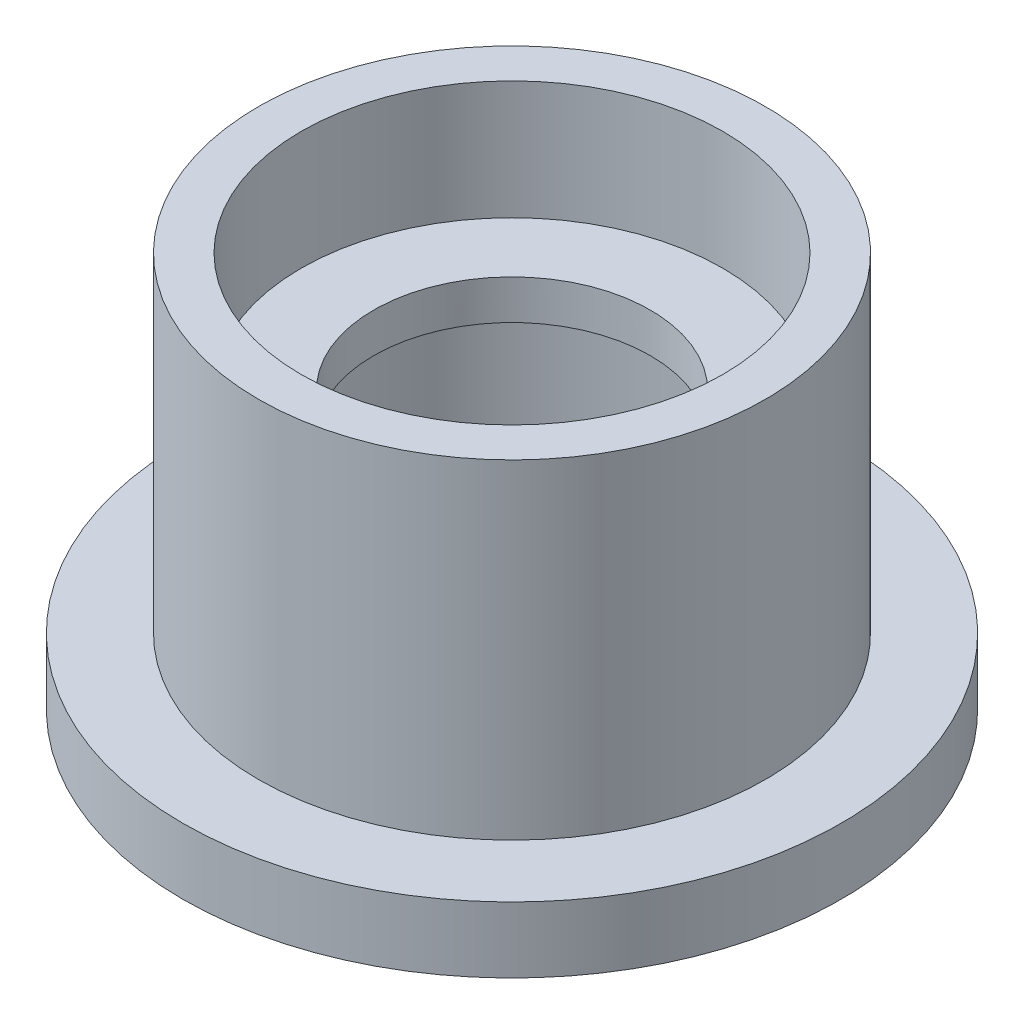
SolidWorks part; units mm, degrees
ref_plane "Front Plane" through (0, 0, 0) normal (0, 0, 1) x (1, 0, 0)
ref_plane "Top Plane" through (0, 0, 0) normal (0, 1, 0) x (1, 0, 0)
ref_plane "Right Plane" through (0, 0, 0) normal (1, 0, 0) x (0, 0, -1)
sketch "Sketch1" plane through (0, 0, 0) normal (0, 1, 0) x (1, 0, 0)
  circle A0 centre (0, 0) radius 25
  dimension "D1" = 50
extrude "Boss-Extrude1" add sketch "Sketch1" along normal blind 30
sketch "Sketch2" plane through (0, 30, 0) normal (0, 1, 0) x (1, 0, 0)
  circle A0 centre (0, 0) radius 19.25
  dimension "D1" = 38.5
extrude "Cut-Extrude1" cut sketch "Sketch2" against normal offset from surface (25 mm away) 5 flip side to cut up to face at (0, 0, 25)
sketch "Sketch3" plane through (0, 30, 0) normal (0, 1, 0) x (1, 0, 0)
  circle A0 centre (0, 0) radius 16
  dimension "D1" = 32
extrude "Cut-Extrude2" cut sketch "Sketch3" against normal blind 9
sketch "Sketch4" plane through (0, 21, 0) normal (0, 1, 0) x (1, 0, 0)
  circle A0 centre (0, 0) radius 10.5
  dimension "D1" = 21
extrude "Cut-Extrude3" cut sketch "Sketch4" against normal through all
sketch "Sketch5" plane through (0, 0, 0) normal (0, -1, 0) x (1, 0, 0)
  circle A0 centre (0, 0) radius 16
  dimension "D1" = 32
extrude "Cut-Extrude4" cut sketch "Sketch5" against normal blind 18
